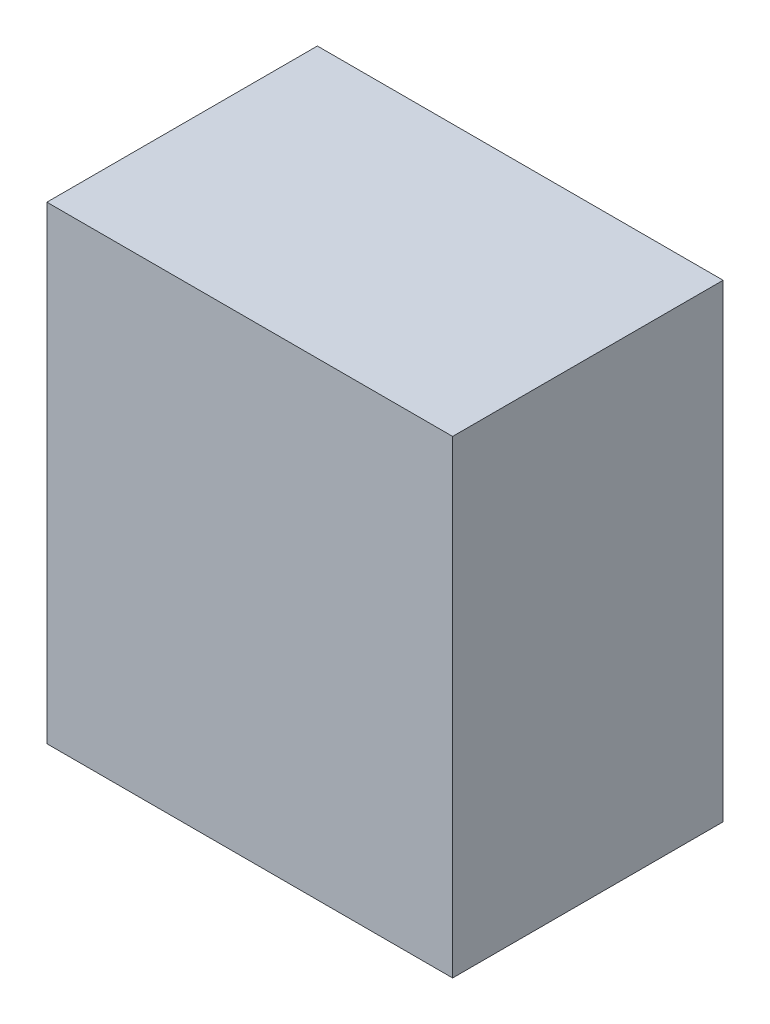
SolidWorks part; units mm, degrees
ref_plane "Front Plane" through (0, 0, 0) normal (0, 0, 1) x (1, 0, 0)
ref_plane "Top Plane" through (0, 0, 0) normal (0, 1, 0) x (1, 0, 0)
ref_plane "Right Plane" through (0, 0, 0) normal (1, 0, 0) x (0, 0, -1)
sketch "Sketch1" plane through (0, 0, 0) normal (0, 1, 0) x (1, 0, 0)
  line L1 (-375, -250) -> (375, -250)
  line L2 (-375, -250) -> (-375, 250)
  line L3 (-375, 250) -> (375, 250)
  line L4 (375, -250) -> (375, 250)
  line L5 (-375, -250) -> (375, 250) construction
  line L6 (-375, 250) -> (375, -250) construction
  point P0 (0, 0)
  dimension "D1" = 750
  dimension "D2" = 500
extrude "Boss-Extrude1" add sketch "Sketch1" along normal blind 807 and the other way blind 60
